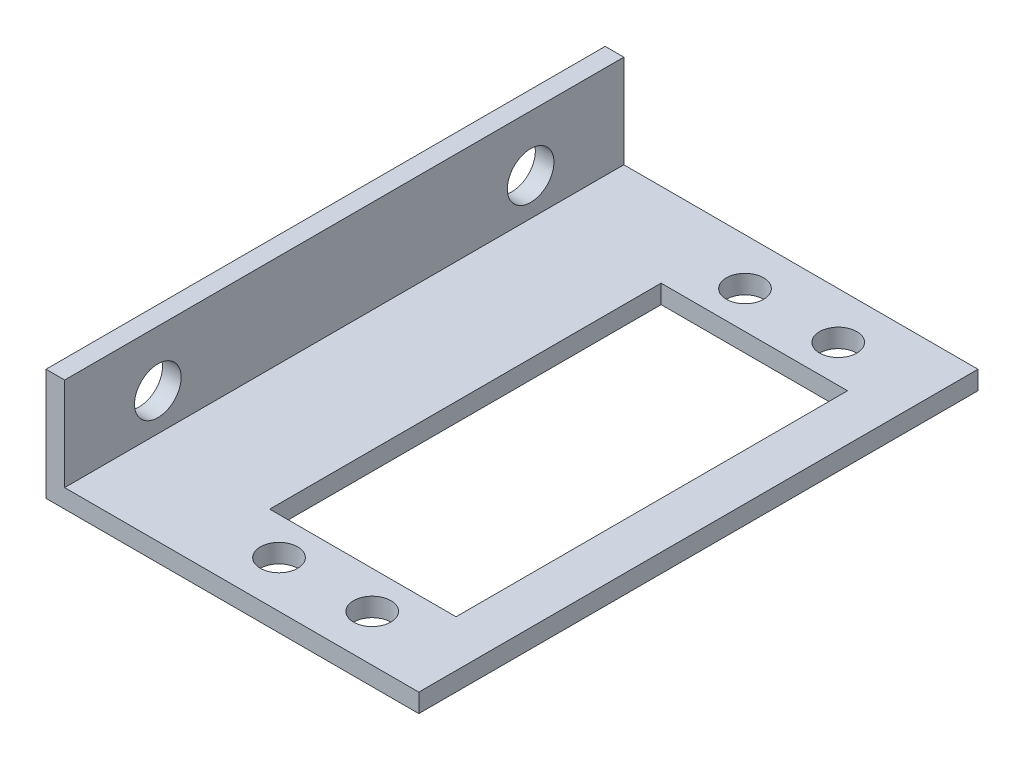
SolidWorks part; units mm, degrees
ref_plane "Alzado" through (0, 0, 0) normal (0, 0, 1) x (1, 0, 0)
ref_plane "Planta" through (0, 0, 0) normal (0, 1, 0) x (1, 0, 0)
ref_plane "Vista lateral" through (0, 0, 0) normal (1, 0, 0) x (0, 0, -1)
sketch "Croquis2" plane through (0, 0, 0) normal (0, 0, 1) x (1, 0, 0)
  line L0 (22.2221, 0) -> (-17.7779, 0)
  line L1 (-17.7779, 0) -> (-17.7779, 12)
  line L2 (-17.7779, 12) -> (-15.7779, 12)
  line L3 (-15.7779, 12) -> (-15.7779, 2)
  line L4 (-15.7779, 2) -> (22.2221, 2)
  line L5 (22.2221, 2) -> (22.2221, 0)
  dimension "D1" = 40
  dimension "D2" = 12
  dimension "D3" = 2
  dimension "D4" = 2
extrude "Saliente-Extruir1" add sketch "Croquis2" along normal blind 60
sketch "Croquis3" plane through (-17.7779, 0, 0) normal (-1, 0, 0) x (0, 0, 1)
  line L0 (0, 12) -> (0, 0) construction
  line L1 (60, 0) -> (0, 0) construction
  circle A0 centre (10, 6) radius 2.5
  circle A1 centre (50, 6) radius 2.5
  point P6 (0, 6)
  point P9 (30, 0)
  dimension "D3" = 5
  dimension "D4" = 5
  dimension "D1" = 20
  dimension "D2" = 20
extrude "Cortar-Extruir1" cut sketch "Croquis3" against normal blind 60
sketch "Croquis4" plane through (0, 0, 0) normal (0, -1, 0) x (1, 0, 0)
  line L0 (-17.7779, 0) -> (22.2221, 0) construction
  line L1 (-2.7779, 51) -> (17.2221, 51)
  line L2 (-2.7779, 51) -> (-2.7779, 9)
  line L3 (-2.7779, 9) -> (17.2221, 9)
  line L4 (17.2221, 51) -> (17.2221, 9)
  line L5 (-2.7779, 51) -> (17.2221, 9) construction
  line L6 (-2.7779, 9) -> (17.2221, 51) construction
  circle A0 centre (2.2221, 55) radius 2
  circle A1 centre (12.2221, 55) radius 2
  circle A2 centre (2.2221, 5) radius 2
  circle A3 centre (12.2221, 5) radius 2
  point P0 (-2.7779, 30)
  point P16 (0, 0)
  point P19 (0, 0)
  point P20 (0, 0)
  point P21 (0, 0)
  point P22 (0, 0)
  dimension "D5" = 4
  dimension "D6" = 4
  dimension "D7" = 4
  dimension "D8" = 4
  dimension "D1" = 20
  dimension "D2" = 42
  dimension "D3" = 5
  dimension "D4" = 9
  dimension "D9" = 10
  dimension "D10" = 10
  dimension "D11" = 5
  dimension "D12" = 5
  dimension "D13" = 5
extrude "Cortar-Extruir2" cut sketch "Croquis4" against normal blind 60
